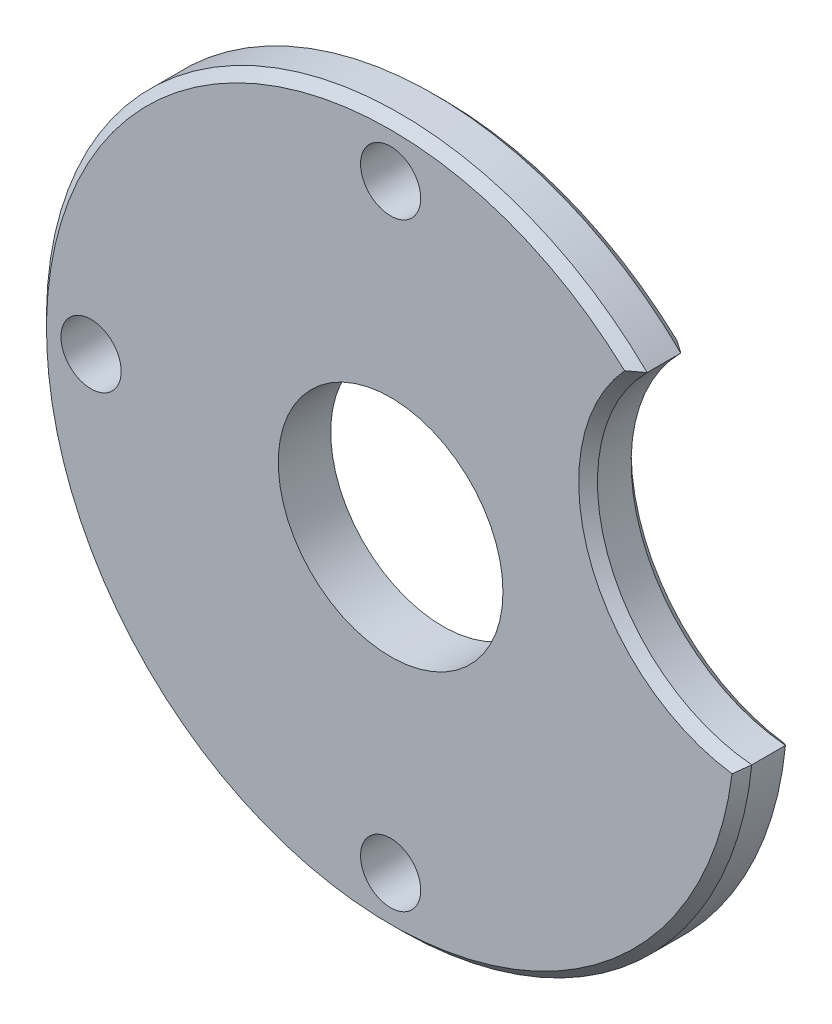
SolidWorks part; units mm, degrees
material "Nylon 101"
ref_plane "Front Plane" through (0, 0, 0) normal (0, 0, 1) x (1, 0, 0)
ref_plane "Top Plane" through (0, 0, 0) normal (0, 1, 0) x (1, 0, 0)
ref_plane "Right Plane" through (0, 0, 0) normal (1, 0, 0) x (0, 0, -1)
sketch "Sketch1" plane through (0, 0, 0) normal (0, 0, 1) x (1, 0, 0)
  line L0 (0, 0) -> (31.0287, 11.2935) construction
  line L1 (0, 25.4) -> (0, 0) construction
  circle A0 centre (0, 0) radius 29.972
  circle A1 centre (31.0287, 11.2935) radius 14.2875
  circle A2 centre (0, 0) radius 9.525
  circle A3 centre (0, 0) radius 25.4 construction
  circle A4 centre (0, 25.4) radius 2.5527
  circle A5 centre (-25.4, 0) radius 2.5527
  circle A6 centre (0, -25.4) radius 2.5527
  dimension "D1" = 59.944
  dimension "D3" = 28.575
  dimension "D4" = 19.05
  dimension "D5" = 50.8
  dimension "D6" = 5.1054
  dimension "D7" = 5.1054
  dimension "D8" = 5.1054
  dimension "D2" = 33.02
  dimension "D9" = 70
extrude "Boss-Extrude1" add sketch "Sketch1" along normal blind 4.445 contours A1 A0 A6 A5 A4 A2
chamfer "Chamfer1" distance 0.7937 angle 45 2 edges at (17.6028, 6.4069, 4.445) (-28.1645, -10.251, 4.445)
chamfer "Chamfer2" distance 0.7937 angle 45 2 edges at (17.6028, 6.4069, 0) (-28.1645, -10.251, 0)
